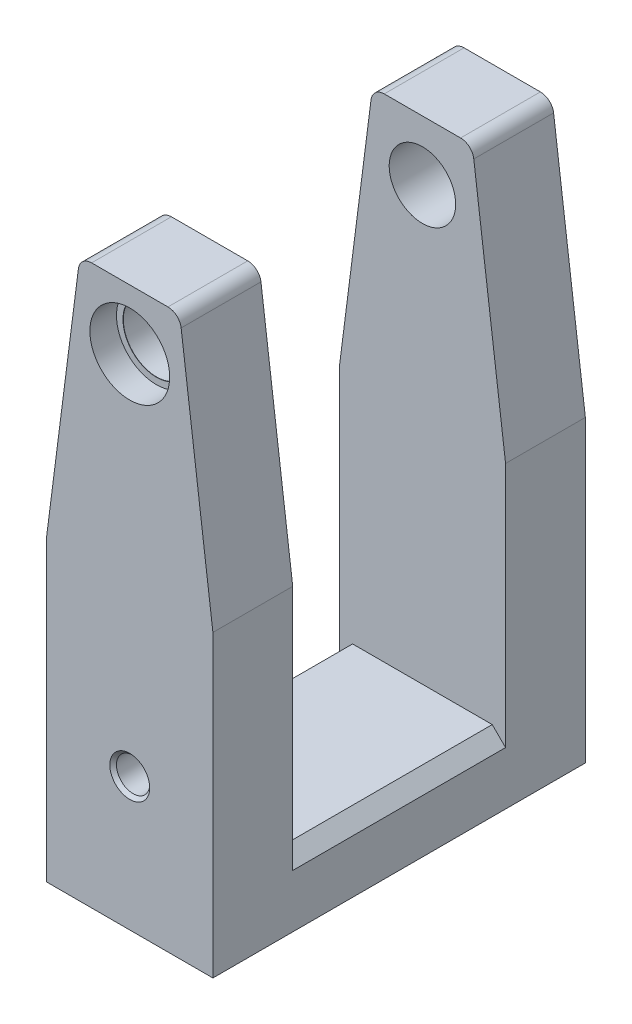
SolidWorks part; units mm, degrees
ref_plane "Front Plane" through (0, 0, 0) normal (0, 0, 1) x (1, 0, 0)
ref_plane "Top Plane" through (0, 0, 0) normal (0, 1, 0) x (1, 0, 0)
ref_plane "Right Plane" through (0, 0, 0) normal (1, 0, 0) x (0, 0, -1)
sketch "Sketch3" plane through (0, 0, 0) normal (0, 0, 1) x (1, 0, 0)
  line L0 (12.5, 0) -> (-12.5, 0)
  line L1 (-12.5, 0) -> (-12.5, 45)
  line L2 (-12.5, 45) -> (-7.5, 84)
  line L3 (-7.5, 84) -> (7.5, 84)
  line L4 (7.5, 84) -> (12.5, 45)
  line L5 (12.5, 45) -> (12.5, 0)
  line L6 (0, 0) -> (0, 84) construction
  dimension "D1" = 25
  dimension "D2" = 15
  dimension "D3" = 84
  dimension "D4" = 45
extrude "Boss-Extrude3" add sketch "Sketch3" along normal mid plane 56
sketch "Sketch4" plane through (12.5, 0, 0) normal (1, 0, 0) x (0, 0, -1)
  line L0 (-28, 84) -> (28, 84) construction
  line L1 (-16, 84) -> (16, 84)
  line L2 (-16, 84) -> (-16, 10)
  line L3 (-16, 10) -> (16, 10)
  line L4 (16, 84) -> (16, 10)
  line L5 (28, 45) -> (28, 84) construction
  line L6 (-28, 0) -> (28, 0) construction
  dimension "D1" = 12
  dimension "D2" = 32
  dimension "D3" = 10
extrude "Cut-Extrude2" cut sketch "Sketch4" against normal through all
hole_wizard "CBORE for M4 Hex Socket Head Cap Screw1" positions "Sketch5" profile "Sketch7" counterbore size "M4" standard "ISO"
sketch "Sketch5" plane through (0, 0, 28) normal (0, 0, 1) x (1, 0, 0)
  line L0 (0, 84) -> (0, 75) construction
  line L1 (7.5, 84) -> (-7.5, 84) construction
  point P0 (0, 75)
  dimension "D1" = 9
sketch "Sketch7" plane through (0, 75, 28) normal (1, 0, 0) x (0, -1, 0)
  line L0 (0, 0) -> (0, 23.0043)
  line L1 (0, 23.0043) -> (5, 20)
  line L2 (5, 20) -> (5, 4.025)
  line L3 (5, 4.025) -> (5.025, 4)
  line L4 (5.025, 4) -> (6, 4)
  line L5 (6, 4) -> (6, 0)
  line L6 (6, 0) -> (0, 0)
  line L9 (-5, 4.025) -> (-5.025, 4) construction
  line L10 (0, 23.0043) -> (-5, 20) construction
  line L11 (0, -6.35) -> (0, 107.95) construction
  dimension "Hole Dia." = 10
  dimension "Hole Depth" = 20
  dimension "C'Bore Dia." = 12
  dimension "C'Bore Depth" = 4
  dimension "Mid C'Sink Dia." = 10.05
  dimension "Mid C'Sink Angle" = 90
  dimension "Drill Angle" = 118
mirror "Mirror1" about plane through (0, 0, 0) normal (0, 0, 1) of "CBORE for M4 Hex Socket Head Cap Screw1"
hole_wizard "M6 Tapped Hole1" positions "Sketch17" profile "Sketch11" tap size "M6" standard "ISO"
sketch "Sketch17" plane through (0, 0, 28) normal (0, 0, 1) x (1, 0, 0)
  line L0 (0, 20) -> (0, 0) construction
  point P0 (0, 20)
  dimension "D1" = 20
sketch "Sketch11" plane through (0, 20, 28) normal (1, 0, 0) x (0, -1, 0)
  line L0 (0, 0) -> (0, 28.5022)
  line L1 (0, 28.5022) -> (2.5, 27)
  line L2 (2.5, 27) -> (2.5, 0.5)
  line L3 (2.5, 0.5) -> (3, 0)
  line L5 (3, 0) -> (0, 0)
  line L6 (-2.5, 0.5) -> (-3, 0) construction
  line L10 (0, 28.5022) -> (-2.5, 27) construction
  line L11 (0, -6.35) -> (0, 107.95) construction
  dimension "Tap Drill Dia." = 5
  dimension "Tap Drill Depth" = 27
  dimension "Near C'Sink Dia." = 6
  dimension "Near C'Sink Angle" = 90
  dimension "Drill Angle" = 118
cosmetic thread "Hole Thread1" parameters "D1"=12, "D2"=6
chamfer "Chamfer1" distance 2 angle 45 2 edges at (-12.5, 10, 0) (12.5, 10, 0)
fillet "Fillet2" radius 2 4 edges at (7.5, 84, -22) (-7.5, 84, 22) (7.5, 84, 22) (-7.5, 84, -22)
